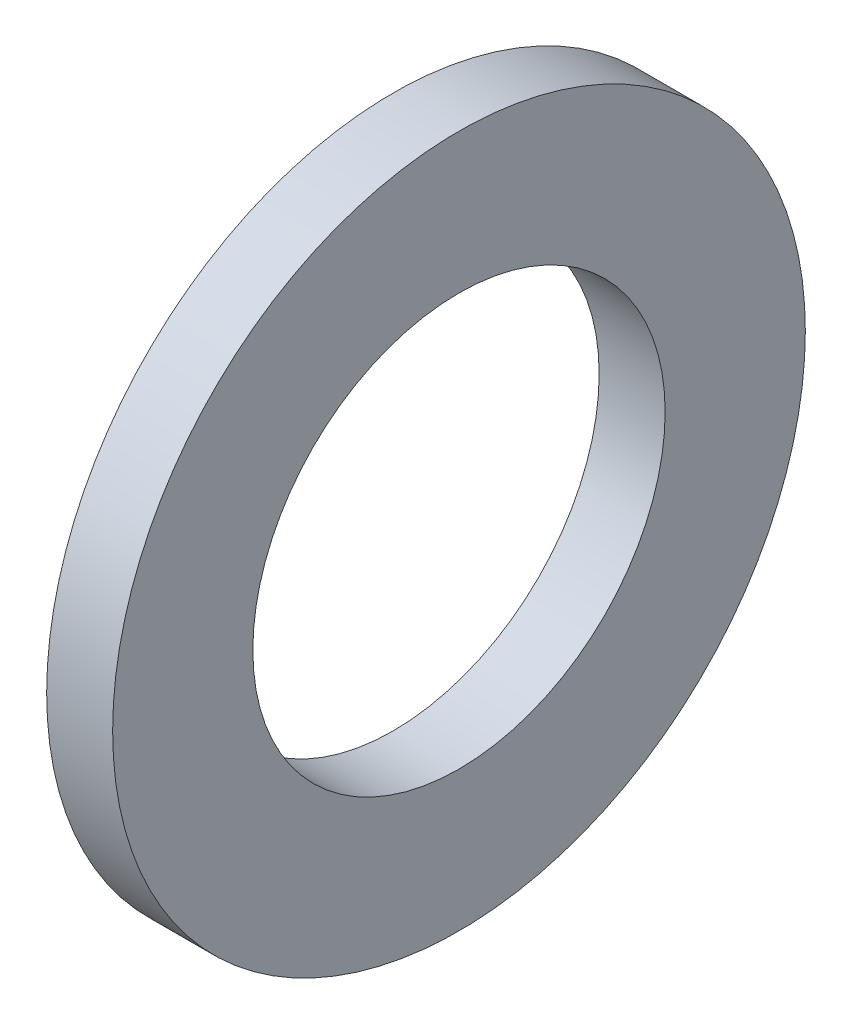
SolidWorks part; units mm, degrees
ref_plane "前视基准面" through (0, 0, 0) normal (0, 0, 1) x (1, 0, 0)
ref_plane "上视基准面" through (0, 0, 0) normal (0, 1, 0) x (1, 0, 0)
ref_plane "右视基准面" through (0, 0, 0) normal (1, 0, 0) x (0, 0, -1)
sketch "草图1" plane through (0, 0, 0) normal (1, 0, 0) x (0, 0, -1)
  circle A0 centre (0, 0) radius 12.5
  circle A1 centre (0, 0) radius 21
  dimension "D1" = 25
  dimension "D2" = 42
extrude "凸台-拉伸1" add sketch "草图1" along normal blind 4
